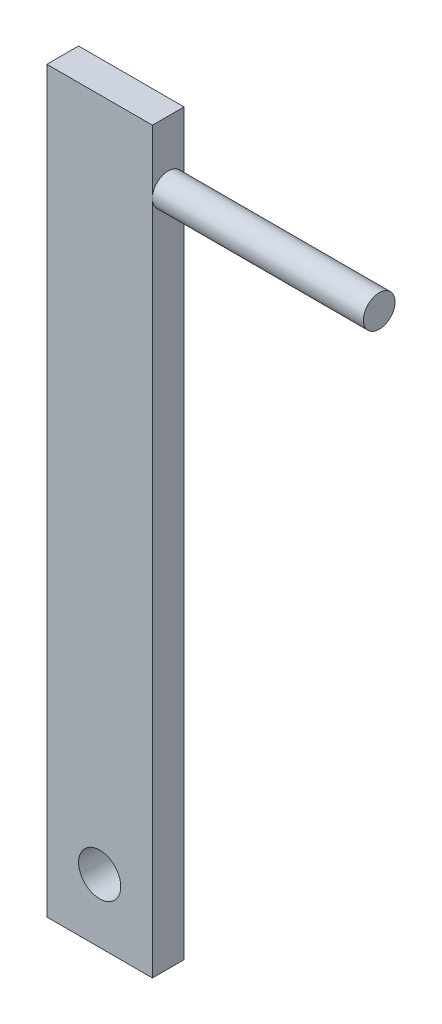
SolidWorks part; units mm, degrees
ref_plane "Front Plane" through (0, 0, 0) normal (0, 0, 1) x (1, 0, 0)
ref_plane "Top Plane" through (0, 0, 0) normal (0, 1, 0) x (1, 0, 0)
ref_plane "Right Plane" through (0, 0, 0) normal (1, 0, 0) x (0, 0, -1)
sketch "Sketch1" plane through (0, 0, 0) normal (0, 1, 0) x (1, 0, 0)
  line L1 (0, 0) -> (5, 0)
  line L2 (0, 0) -> (0, -1.5)
  line L3 (0, -1.5) -> (5, -1.5)
  line L4 (5, 0) -> (5, -1.5)
  dimension "D1" = 1.5
  dimension "D2" = 5
extrude "Boss-Extrude1" add sketch "Sketch1" along normal blind 35
sketch "Sketch2" plane through (0, 0, 0) normal (0, 0, -1) x (-1, 0, 0)
  line L0 (-5, 0) -> (0, 0) construction
  line L1 (-2.5, 35) -> (-2.5, -0.6003) construction
  line L2 (-5, 35) -> (0, 35) construction
  circle A0 centre (-2.5, 3) radius 1
  dimension "D1" = 2
  dimension "D2" = 3
extrude "Cut-Extrude1" cut sketch "Sketch2" against normal through all both and the other way through all
sketch "Sketch3" plane through (5, 0, 0) normal (1, 0, 0) x (0, 0, -1)
  line L0 (-0.75, 35) -> (-0.75, 0) construction
  line L1 (-1.5, 35) -> (0, 35) construction
  line L2 (-1.5, 0) -> (0, 0) construction
  circle A0 centre (-0.75, 32) radius 0.75
  dimension "D1" = 1.5
  dimension "D2" = 3
extrude "Boss-Extrude2" add sketch "Sketch3" along normal blind 10
